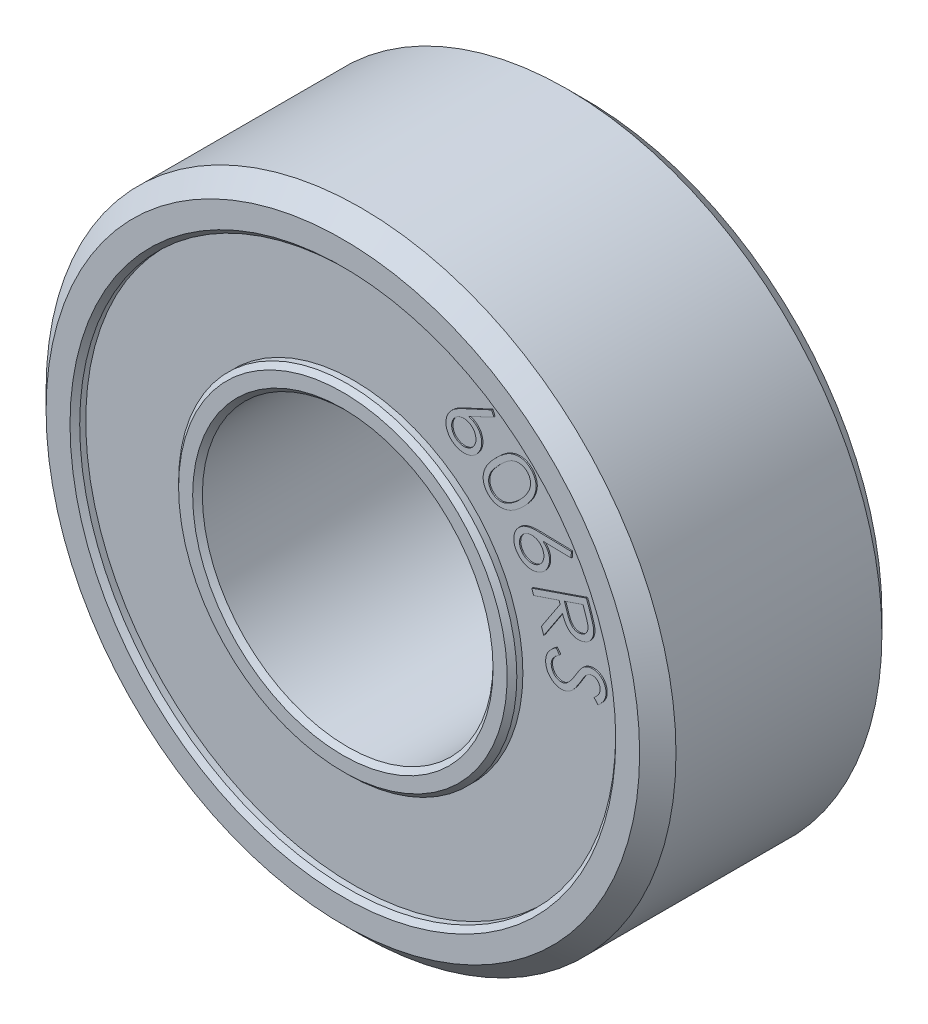
SolidWorks part; units mm, degrees
ref_plane "Front Plane" through (0, 0, 0) normal (0, 0, 1) x (1, 0, 0)
ref_plane "Top Plane" through (0, 0, 0) normal (0, 1, 0) x (1, 0, 0)
ref_plane "Right Plane" through (0, 0, 0) normal (1, 0, 0) x (0, 0, -1)
sketch "Sketch3" plane through (0, 0, 0) normal (0, 1, 0) x (1, 0, 0)
  line L0 (0, 0) -> (-6.5, 0) construction
  line L1 (0, 0) -> (0, 2.5) construction
  line L2 (0, 2.5) -> (-6.5, 2.5) construction
  line L3 (-6.5, 2.5) -> (-6.5, 0) construction
  line L4 (-3, 2.5) -> (-3, -2.5)
  line L5 (-3, 2.5) -> (-3.4905, 2.5)
  line L6 (-6.5, -2.5) -> (-6.5, 2.5)
  line L7 (-6.5, 2.5) -> (-5.5315, 2.5)
  line L8 (-5.5315, 2.5) -> (-5.5315, 2.275)
  line L9 (-5.5315, 2.275) -> (-3.4905, 2.275)
  line L10 (-3.4905, 2.275) -> (-3.4905, 2.5)
  line L11 (-3, -2.5) -> (-3.4905, -2.5)
  line L12 (-3.4905, -2.275) -> (-3.4905, -2.5)
  line L13 (-5.5315, -2.275) -> (-3.4905, -2.275)
  line L14 (-5.5315, -2.5) -> (-5.5315, -2.275)
  line L15 (-6.5, -2.5) -> (-5.5315, -2.5)
  point P12 (-3, 0)
  dimension "D1" = 6.5
  dimension "D2" = 2.5
  dimension "D3" = 3
  dimension "D4" = 3.4905
  dimension "D5" = 5.5315
  dimension "D6" = 0.225
revolve "Revolve1" add sketch "Sketch3" angle 360 about L1
chamfer "Chamfer1" distance 0.375 angle 45 2 edges at (6.5, 0, -2.5) (6.5, 0, 2.5)
chamfer "Chamfer2" distance 0.1 angle 45 6 edges at (3.4905, 0, 2.5) (3, 0, 2.5) (3, 0, -2.5) (3.4905, 0, -2.5) (5.5315, 0, 2.5) (5.5315, 0, -2.5)
sketch "Sketch4" plane through (0, 0, 2.275) normal (0, 0, 1) x (1, 0, 0)
  circle A0 centre (0, 0) radius 4.0625 construction
  text T0 "606RS" font "Century Gothic" height 1.2
  dimension "D1" = 8.125
extrude "Boss-Extrude1" add sketch "Sketch4" along normal blind 0.025
sketch "Sketch5" plane through (0, 0, -2.275) normal (0, 0, -1) x (-1, 0, 0)
  circle A0 centre (0, 0) radius 4.0625 construction
  text T0 "606RS" font "Century Gothic" height 1.2
  dimension "D1" = 8.125
extrude "Boss-Extrude2" add sketch "Sketch5" along normal blind 0.025
equation "\"InnerDiameter\"= 6mm"
equation "\"OuterDiameter\" = 13mm"
equation "\"Width\"= 5mm"
equation "\"D1@Sketch3\"= 0.5 * \"OuterDiameter\""
equation "\"D2@Sketch3\"= 0.5 * \"Width\""
equation "\"D3@Sketch3\"=0.5 * \"InnerDiameter\""
equation "\"D4@Sketch3\"= (\"OuterDiameter\" * 0.537 )/2"
equation "\"D5@Sketch3\"= (\"OuterDiameter\" *  0.851)/2"
equation "\"D6@Sketch3\"=\"Width\" * 0.045"
equation "\"D1@Chamfer1\"=\"Width\" * 0.075"
equation "\"D1@Chamfer2\"=\"Width\"*0.02"
equation "\"D1@Sketch4\"=\"OuterDiameter\"*0.625"
equation "\"D1@Boss-Extrude1\"=\"Width\"* 0.005"
equation "\"D1@Sketch5\"=\"OuterDiameter\" *0.625"
equation "\"D1@Boss-Extrude2\"=\"Width\"*0.005"
